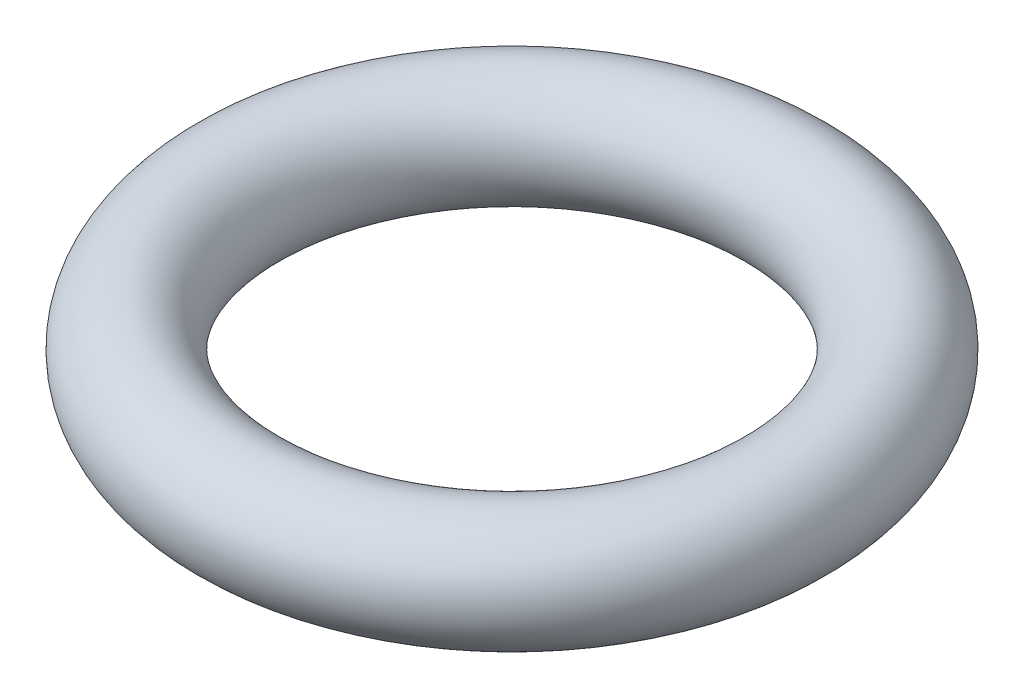
SolidWorks part; units mm, degrees
ref_plane "Front" through (0, 0, 0) normal (0, 0, 1) x (1, 0, 0)
ref_plane "Top" through (0, 0, 0) normal (0, 1, 0) x (1, 0, 0)
ref_plane "Right" through (0, 0, 0) normal (1, 0, 0) x (0, 0, -1)
sketch "Sketch1" plane through (0, 0, 0) normal (0, 0, 1) x (1, 0, 0)
  line L0 (0, 0) -> (12, 0) construction
  line L1 (0, 20.495) -> (0, -38.3701) construction
  circle A0 centre (12, 0) radius 2.5
  dimension "D1" = 12
  dimension "D2" = 5
revolve "Revolve1" add sketch "Sketch1" angle 360 about L1
